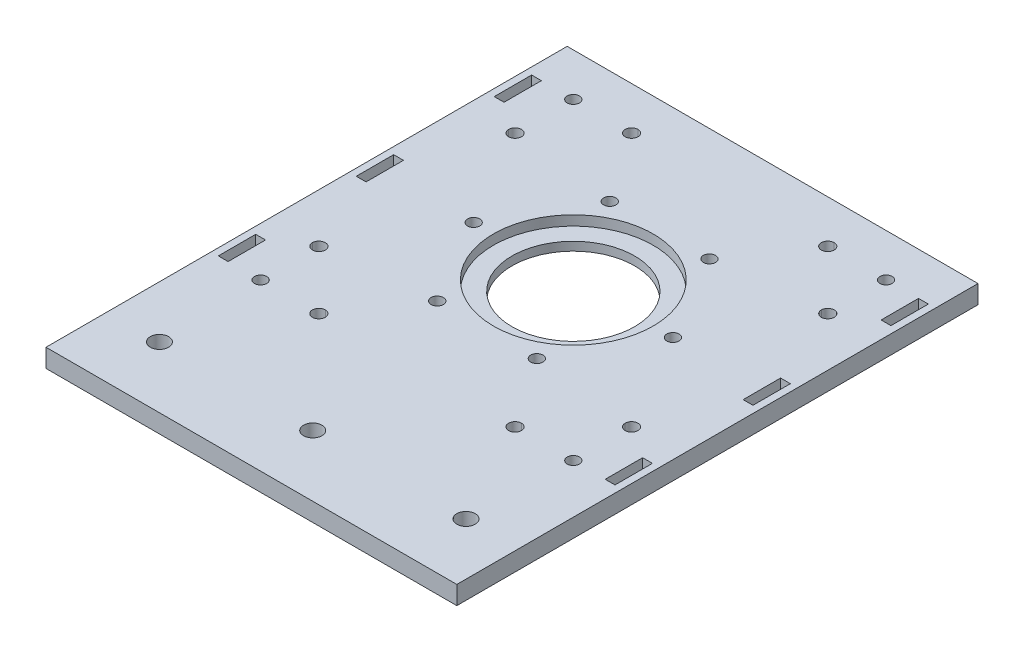
SolidWorks part; units mm, degrees
other "Markup1"
sketch "Sketch12" plane through (-65, 37, 65) normal (-0.0511, -0.9215, 0.3851) x (-0.6026, -0.2791, -0.7477)
material "Acrylic (Medium-high impact)"
ref_plane "Front Plane" through (0, 0, 0) normal (0, 0, 1) x (1, 0, 0)
ref_plane "Top Plane" through (0, 0, 0) normal (0, 1, 0) x (1, 0, 0)
ref_plane "Right Plane" through (0, 0, 0) normal (1, 0, 0) x (0, 0, -1)
sketch "Sketch15" plane through (0, 0, 0) normal (0, 1, 0) x (1, 0, 0)
  line L0 (65, 65) -> (-65, 65)
  line L1 (-65, 65) -> (-65, -65)
  line L2 (-65, -65) -> (65, -65)
  line L3 (65, 65) -> (65, -65)
  line L4 (0, 0) -> (32.5, 0) construction
  line L5 (28.1458, -16.25) -> (0, 0) construction
  arc A0 (0, -65) -> (0, 65) centre (0, 0) ccw construction
  circle A1 centre (0, 0) radius 32.5 construction
  circle A6 centre (0, 0) radius 20
  circle A7 centre (32.5, 0) radius 2
  circle A8 centre (16.25, -28.1458) radius 2
  circle A9 centre (-16.25, -28.1458) radius 2
  circle A10 centre (-32.5, 0) radius 2
  circle A11 centre (-16.25, 28.1458) radius 2
  circle A12 centre (16.25, 28.1458) radius 2
  point P26 (0, 0)
  dimension "D1" = 130
  dimension "D4" = 65
  dimension "D6" = 4
  dimension "D7" = 40
  dimension "D8" = 6
  dimension "D2" = 65
  dimension "D3" = 65
  dimension "D5" = 30
  dimension "D9" = 16.25
extrude "Boss-Extrude1" add sketch "Sketch15" along normal blind 6
sketch "Sketch16" plane through (0, 6, 0) normal (0, 1, 0) x (1, 0, 0)
  circle A0 centre (0, 0) radius 26.05
  dimension "D1" = 52.1
extrude "Cut-Extrude6" cut sketch "Sketch16" against normal blind 3.2
sketch "Sketch17" plane through (0, 0, 0) normal (0, -1, 0) x (1, 0, 0)
  line L0 (-9.6164, 0) -> (10.7367, 0) construction
  line L1 (0, -10.0832) -> (0, 9.7097) construction
  line L2 (-65, 65) -> (65, 65) construction
  line L3 (41, 61) -> (61, 61)
  line L4 (41, 61) -> (41, 41)
  line L5 (41, 41) -> (61, 41)
  line L6 (61, 61) -> (61, 41)
  line L7 (41, 61) -> (61, 41) construction
  line L8 (41, 41) -> (61, 61) construction
  line L9 (65, 65) -> (65, -65) construction
  line L10 (-41, 41) -> (-61, 61) construction
  line L11 (-41, 61) -> (-61, 41) construction
  line L12 (-41, 41) -> (-61, 41)
  line L13 (-61, 61) -> (-61, 41)
  line L14 (-41, 61) -> (-61, 61)
  line L15 (-41, 61) -> (-41, 41)
  line L16 (-41, -61) -> (-61, -41) construction
  line L17 (-41, -41) -> (-61, -61) construction
  line L18 (41, -41) -> (61, -61) construction
  line L19 (41, -61) -> (61, -41) construction
  line L20 (-41, -61) -> (-41, -41)
  line L21 (-41, -61) -> (-61, -61)
  line L22 (-61, -61) -> (-61, -41)
  line L23 (-41, -41) -> (-61, -41)
  line L24 (61, -61) -> (61, -41)
  line L25 (41, -41) -> (61, -41)
  line L26 (41, -61) -> (41, -41)
  line L27 (41, -61) -> (61, -61)
  line L28 (51, 32) -> (51, 31.999) construction
  line L29 (53.1, 32) -> (53.1, 31.999)
  line L30 (48.9, 32) -> (48.9, 31.999)
  line L31 (32, 51) -> (31.999, 51) construction
  line L32 (32, 53.1) -> (31.999, 53.1)
  line L33 (32, 48.9) -> (31.999, 48.9)
  line L34 (-32, 48.9) -> (-31.999, 48.9)
  line L35 (-32, 53.1) -> (-31.999, 53.1)
  line L36 (-48.9, 32) -> (-48.9, 31.999)
  line L37 (-53.1, 32) -> (-53.1, 31.999)
  line L38 (32, -48.9) -> (31.999, -48.9)
  line L39 (32, -53.1) -> (31.999, -53.1)
  line L40 (48.9, -32) -> (48.9, -31.999)
  line L41 (53.1, -32) -> (53.1, -31.999)
  line L42 (-53.1, -32) -> (-53.1, -31.999)
  line L43 (-48.9, -32) -> (-48.9, -31.999)
  line L44 (-32, -53.1) -> (-31.999, -53.1)
  line L45 (-32, -48.9) -> (-31.999, -48.9)
  arc A0 (53.1, 32) -> (48.9, 32) centre (51, 32) ccw
  arc A1 (53.1, 31.999) -> (48.9, 31.999) centre (51, 31.999) cw
  circle A2 centre (51, 51) radius 2
  arc A3 (32, 53.1) -> (32, 48.9) centre (32, 51) cw
  arc A4 (31.999, 53.1) -> (31.999, 48.9) centre (31.999, 51) ccw
  arc A5 (-32, 53.1) -> (-32, 48.9) centre (-32, 51) ccw
  arc A6 (-31.999, 53.1) -> (-31.999, 48.9) centre (-31.999, 51) cw
  arc A7 (-53.1, 32) -> (-48.9, 32) centre (-51, 32) cw
  arc A8 (-53.1, 31.999) -> (-48.9, 31.999) centre (-51, 31.999) ccw
  circle A9 centre (-51, 51) radius 2
  circle A10 centre (51, -51) radius 2
  arc A11 (32, -53.1) -> (32, -48.9) centre (32, -51) ccw
  arc A12 (31.999, -53.1) -> (31.999, -48.9) centre (31.999, -51) cw
  arc A13 (53.1, -32) -> (48.9, -32) centre (51, -32) cw
  arc A14 (53.1, -31.999) -> (48.9, -31.999) centre (51, -31.999) ccw
  arc A15 (-53.1, -31.999) -> (-48.9, -31.999) centre (-51, -31.999) cw
  arc A16 (-53.1, -32) -> (-48.9, -32) centre (-51, -32) ccw
  arc A17 (-31.999, -53.1) -> (-31.999, -48.9) centre (-31.999, -51) ccw
  arc A18 (-32, -53.1) -> (-32, -48.9) centre (-32, -51) cw
  circle A19 centre (-51, -51) radius 2
  point P1 (51, 51)
  point P26 (51, -51)
  dimension "D9" = 4
  dimension "D1" = 20
  dimension "D2" = 20
  dimension "D3" = 4
  dimension "D4" = 4
  dimension "D5" = 0.001
  dimension "D6" = 9
  dimension "D10" = 0.001
  dimension "D11" = 9
  dimension "D7" = 2.1
  dimension "D8" = 2.1
  dimension "D12" = 2.1
  dimension "D13" = 2.1
extrude "Cut-Extrude7" cut sketch "Sketch17" against normal through all contours A9 | A6 L35 A5 L34 | L37 A8 L36 A7 | A2 | A1 L29 A0 L30 | A10 | L41 A14 L40 A13 | A12 L39 A11 L38 | A18 L44 A17 L45 | A19 | L42 A16 L43 A15 | A3 L33 A4 L32
sketch "Sketch18" plane through (0, 6, 0) normal (0, 1, 0) x (1, 0, 0)
  line L0 (-65, -65) -> (65, -65)
  line L1 (-65, -65) -> (-65, -105)
  line L2 (65, -65) -> (65, -105)
  line L3 (-65, -105) -> (65, -105)
  circle A0 centre (50, -85) radius 3
  circle A1 centre (0, -85) radius 3
  circle A2 centre (-50, -85) radius 3
  dimension "D2" = 6
  dimension "D4" = 50
  dimension "D5" = 20
  dimension "D1" = 40
  dimension "D3" = 50
extrude "Boss-Extrude2" add sketch "Sketch18" against normal up to surface (6 mm away) up to face at (-31.9995, 0, 51)
sketch "Sketch21" plane through (0, 6, 0) normal (0, 1, 0) x (1, 0, 0)
  line L0 (65, 65) -> (-65, 65) construction
  line L1 (-67, 65) -> (-65, 65)
  line L2 (-67, 65) -> (-67, -105)
  line L3 (-67, -105) -> (-65, -105)
  line L4 (-65, 65) -> (-65, -105)
  line L5 (0, -3.3) -> (0, 3.3) construction
  line L6 (67, -105) -> (65, -105)
  line L7 (65, 65) -> (65, -105)
  line L8 (67, 65) -> (65, 65)
  line L9 (67, 65) -> (67, -105)
  dimension "D1" = 2
extrude "Boss-Extrude3" add sketch "Sketch21" against normal up to surface (6 mm away) up to face at (-31.9995, 0, 51)
sketch "Sketch20" plane through (0, 6, 0) normal (0, 1, 0) x (1, 0, 0)
  line L0 (67, 65) -> (-67, 65) construction
  line L1 (-64.7, 51.1) -> (-61.5, 51.1)
  line L2 (-64.7, 51.1) -> (-64.7, 38.9)
  line L3 (-64.7, 38.9) -> (-61.5, 38.9)
  line L4 (-61.5, 51.1) -> (-61.5, 38.9)
  line L5 (-64.7, 51.1) -> (-61.5, 38.9) construction
  line L6 (-64.7, 38.9) -> (-61.5, 51.1) construction
  line L7 (-64.7, 6.1) -> (-61.5, 6.1)
  line L8 (-64.7, 6.1) -> (-64.7, -6.1)
  line L9 (-64.7, -6.1) -> (-61.5, -6.1)
  line L10 (-61.5, 6.1) -> (-61.5, -6.1)
  line L11 (-64.7, 6.1) -> (-61.5, -6.1) construction
  line L12 (-64.7, -6.1) -> (-61.5, 6.1) construction
  line L13 (-64.7, -38.9) -> (-61.5, -38.9)
  line L14 (-64.7, -38.9) -> (-64.7, -51.1)
  line L15 (-64.7, -51.1) -> (-61.5, -51.1)
  line L16 (-61.5, -38.9) -> (-61.5, -51.1)
  line L17 (-64.7, -38.9) -> (-61.5, -51.1) construction
  line L18 (-64.7, -51.1) -> (-61.5, -38.9) construction
  line L19 (0, -3.3) -> (0, 3.3) construction
  line L20 (64.7, -51.1) -> (61.5, -38.9) construction
  line L21 (64.7, -38.9) -> (61.5, -51.1) construction
  line L22 (64.7, -6.1) -> (61.5, 6.1) construction
  line L23 (64.7, 6.1) -> (61.5, -6.1) construction
  line L24 (64.7, 38.9) -> (61.5, 51.1) construction
  line L25 (64.7, 51.1) -> (61.5, 38.9) construction
  line L26 (61.5, -38.9) -> (61.5, -51.1)
  line L27 (64.7, -51.1) -> (61.5, -51.1)
  line L28 (64.7, -38.9) -> (64.7, -51.1)
  line L29 (64.7, -38.9) -> (61.5, -38.9)
  line L30 (61.5, 6.1) -> (61.5, -6.1)
  line L31 (64.7, -6.1) -> (61.5, -6.1)
  line L32 (64.7, 6.1) -> (64.7, -6.1)
  line L33 (64.7, 6.1) -> (61.5, 6.1)
  line L34 (61.5, 51.1) -> (61.5, 38.9)
  line L35 (64.7, 38.9) -> (61.5, 38.9)
  line L36 (64.7, 51.1) -> (64.7, 38.9)
  line L37 (64.7, 51.1) -> (61.5, 51.1)
  circle A0 centre (-51, 51) radius 2 construction
  point P0 (-63.1, 45)
  point P9 (-63.1, 0)
  point P14 (-63.1, -45)
  point P33 (63.1, -45)
  point P34 (63.1, 0)
  point P35 (63.1, 45)
  dimension "D1" = 10.5
  dimension "D2" = 3.2
  dimension "D3" = 12.2
  dimension "D4" = 20
  dimension "D5" = 3.2
  dimension "D6" = 12.2
  dimension "D7" = 3.2
  dimension "D8" = 12.2
  dimension "D9" = 45
  dimension "D10" = 45
extrude "Cut-Extrude8" cut sketch "Sketch20" against normal blind 10
